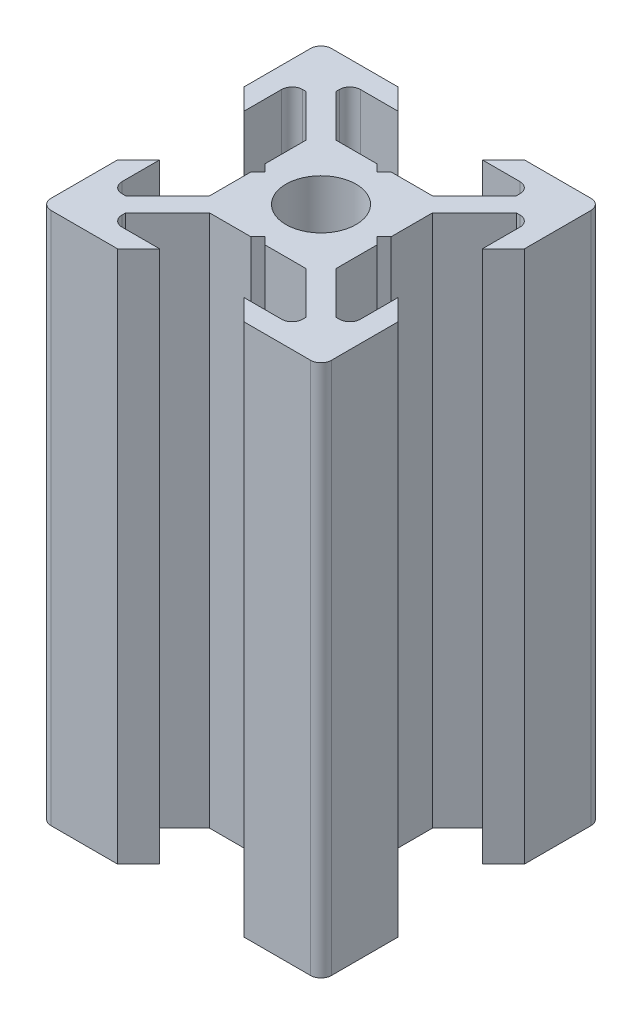
SolidWorks part; units mm, degrees
ref_plane "Face" through (0, 0, 0) normal (0, 0, 1) x (1, 0, 0)
ref_plane "Dessus" through (0, 0, 0) normal (0, 1, 0) x (1, 0, 0)
ref_plane "Droite" through (0, 0, 0) normal (1, 0, 0) x (0, 0, -1)
sketch "Esquisse1" plane through (0, 0, 0) normal (0, 1, 0) x (1, 0, 0)
  line L0 (0, 0) -> (0, 10) construction
  line L1 (0, 0) -> (-10, 0) construction
  line L2 (-10, 0) -> (-10, 10) construction
  line L3 (-10, 10) -> (0, 10) construction
  line L4 (0, 4) -> (-0.5, 4.5)
  line L5 (-0.5, 4.5) -> (-3.4393, 4.5)
  line L6 (-3.4393, 4.5) -> (-6.4393, 7.5)
  line L7 (-6.4393, 7.5) -> (-6.4393, 8.5)
  line L8 (-6.4393, 8.5) -> (-3, 8.5)
  line L9 (-3, 8.5) -> (-4.5, 10)
  line L10 (-4.5, 10) -> (-10, 10)
  line L11 (0, 0) -> (-10, 10) construction
  line L12 (-10, 4.5) -> (-10, 10)
  line L13 (-8.5, 3) -> (-10, 4.5)
  line L14 (-8.5, 6.4393) -> (-8.5, 3)
  line L15 (-7.5, 6.4393) -> (-8.5, 6.4393)
  line L16 (-4.5, 3.4393) -> (-7.5, 6.4393)
  line L17 (-4.5, 0.5) -> (-4.5, 3.4393)
  line L18 (-4, 0) -> (-4.5, 0.5)
  line L19 (0, -4) -> (-0.5, -4.5)
  line L20 (-0.5, -4.5) -> (-3.4393, -4.5)
  line L21 (-4, 0) -> (-4.5, -0.5)
  line L22 (-4.5, -0.5) -> (-4.5, -3.4393)
  line L23 (-4.5, -3.4393) -> (-7.5, -6.4393)
  line L24 (-3.4393, -4.5) -> (-6.4393, -7.5)
  line L25 (-3, -8.5) -> (-4.5, -10)
  line L26 (-6.4393, -8.5) -> (-3, -8.5)
  line L27 (-6.4393, -7.5) -> (-6.4393, -8.5)
  line L28 (-7.5, -6.4393) -> (-8.5, -6.4393)
  line L29 (-4.5, -10) -> (-10, -10)
  line L30 (-10, -4.5) -> (-10, -10)
  line L31 (-8.5, -3) -> (-10, -4.5)
  line L32 (-8.5, -6.4393) -> (-8.5, -3)
  line L33 (8.5, -6.4393) -> (8.5, -3)
  line L34 (8.5, -3) -> (10, -4.5)
  line L35 (10, -4.5) -> (10, -10)
  line L36 (4.5, -10) -> (10, -10)
  line L37 (7.5, -6.4393) -> (8.5, -6.4393)
  line L38 (6.4393, -7.5) -> (6.4393, -8.5)
  line L39 (6.4393, -8.5) -> (3, -8.5)
  line L40 (3, -8.5) -> (4.5, -10)
  line L41 (3.4393, -4.5) -> (6.4393, -7.5)
  line L42 (4.5, -3.4393) -> (7.5, -6.4393)
  line L43 (4.5, -0.5) -> (4.5, -3.4393)
  line L44 (4, 0) -> (4.5, -0.5)
  line L45 (0.5, -4.5) -> (3.4393, -4.5)
  line L46 (0, -4) -> (0.5, -4.5)
  line L47 (4, 0) -> (4.5, 0.5)
  line L48 (4.5, 0.5) -> (4.5, 3.4393)
  line L49 (4.5, 3.4393) -> (7.5, 6.4393)
  line L50 (7.5, 6.4393) -> (8.5, 6.4393)
  line L51 (8.5, 6.4393) -> (8.5, 3)
  line L52 (8.5, 3) -> (10, 4.5)
  line L53 (10, 4.5) -> (10, 10)
  line L54 (4.5, 10) -> (10, 10)
  line L55 (3, 8.5) -> (4.5, 10)
  line L56 (6.4393, 8.5) -> (3, 8.5)
  line L57 (6.4393, 7.5) -> (6.4393, 8.5)
  line L58 (3.4393, 4.5) -> (6.4393, 7.5)
  line L59 (0.5, 4.5) -> (3.4393, 4.5)
  line L60 (0, 4) -> (0.5, 4.5)
  circle A0 centre (0, 0) radius 2.5
  dimension "D10" = 5
  dimension "D1" = 10
  dimension "D2" = 45
  dimension "D3" = 45
  dimension "D4" = 1.5
  dimension "D5" = 7
  dimension "D6" = 1
  dimension "D7" = 4.5
  dimension "D8" = 0.5
  dimension "D9" = 0.75
extrude "Extrusion1" add sketch "Esquisse1" along normal blind 38
fillet "Congé1" radius 0.75 12 edges at (-8.5, 19, -6.4393) (-6.4393, 19, -8.5) (8.5, 19, -6.4393) (6.4393, 19, -8.5) (-8.5, 19, 6.4393) (-6.4393, 19, 8.5) (8.5, 19, 6.4393) (6.4393, 19, 8.5) (10, 19, -10) (-10, 19, -10) (-10, 19, 10) (10, 19, 10)
